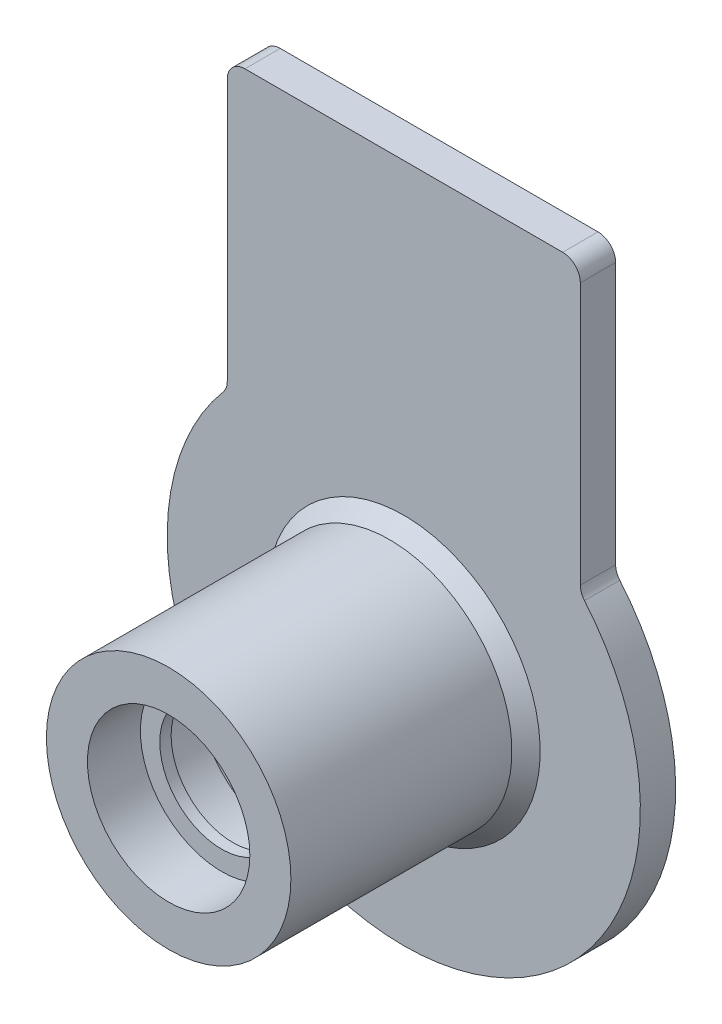
SolidWorks part; units mm, degrees
ref_plane "Front Plane" through (0, 0, 0) normal (0, 0, 1) x (1, 0, 0)
ref_plane "Top Plane" through (0, 0, 0) normal (0, 1, 0) x (1, 0, 0)
ref_plane "Right Plane" through (0, 0, 0) normal (1, 0, 0) x (0, 0, -1)
sketch "Sketch2" plane through (0, 0, 0) normal (0, 1, 0) x (1, 0, 0)
  line L0 (-3.5, -12.32) -> (-3.5, -11.68)
  line L1 (-3.5, -11.68) -> (-4.925, -11.2)
  line L2 (-4.925, -11.2) -> (-4.925, -8.7)
  line L3 (-4.925, -8.7) -> (-3.45, -8.7)
  line L4 (-3.45, -8.7) -> (-3.45, -7.5)
  line L5 (-3.45, -7.5) -> (-5, -7.5)
  line L6 (-3.5, -12.32) -> (-6.925, -12.32)
  line L7 (-6.925, -12.32) -> (-6.925, -2)
  line L8 (-5, -7.5) -> (-5, 0)
  line L12 (-13.4, 0) -> (-13.4, -2)
  line L13 (-13.4, -2) -> (-6.925, -2)
  line L14 (0, 0) -> (0, -12.32) construction
  line L15 (13.4, -2) -> (6.925, -2) construction
  line L16 (13.4, 0) -> (13.4, -2) construction
  line L20 (5, -7.5) -> (5, 0) construction
  line L21 (6.925, -12.32) -> (6.925, -2) construction
  line L22 (3.5, -12.32) -> (6.925, -12.32) construction
  line L23 (3.45, -7.5) -> (5, -7.5) construction
  line L24 (3.45, -8.7) -> (3.45, -7.5) construction
  line L25 (4.925, -8.7) -> (3.45, -8.7) construction
  line L26 (4.925, -11.2) -> (4.925, -8.7) construction
  line L27 (3.5, -11.68) -> (4.925, -11.2) construction
  line L28 (3.5, -12.32) -> (3.5, -11.68) construction
  line L31 (-5, 0) -> (-13.4, 0)
  line L34 (5, 0) -> (13.4, 0) construction
other "AlignGroup1"
other "AlignGroup2" parameters "D1"=6.1239, "D2"=15.6, "D3"=6.4543, "D4"=0.8, "D5"=10.0543, "D6"=6, "D7"=8.1501, "D8"=3.5773, "D9"=31.118, "D10"=2.5, "D11"=0.8, "D12"=5.3492, "D13"=1.7, "D14"=0.819, "D15"=0.3, "D16"=2.2
revolve "Revolve1" add sketch "Sketch2" angle 360 about L14
sketch "Sketch3" plane through (0, 0, 2) normal (0, 0, 1) x (1, 0, 0)
  line L0 (10, 8.9196) -> (10, 25.1216)
  line L1 (10, 25.1216) -> (-10, 25.1216)
  line L2 (-10, 25.1216) -> (-10, 8.9196)
  line L3 (0, 0) -> (-8, 8.1216) construction
  line L4 (-8, 8.1216) -> (-10, 8.1216) construction
  circle A0 centre (0, 0) radius 13.4 construction
  arc A1 (-10, 8.9196) -> (10, 8.9196) centre (0, 0) cw
  circle A2 centre (0, 0) radius 11.4 construction
  dimension "D2" = 22.8
  dimension "D1" = 20
  dimension "D3" = 2
  dimension "D4" = 17
extrude "Boss-Extrude1" add sketch "Sketch3" against normal up to surface (2 mm away) up to face at (-13.4, 0, 0)
fillet "Fillet2" radius 1 4 edges at (10, 8.9196, 1) (10, 25.1216, 1) (-10, 8.9196, 1) (-10, 25.1216, 1)
chamfer "Chamfer1" distance 0.8 angle 45 1 edges at (-6.925, 0, 2)
sketch "Sketch4" plane through (0, 0, 12.32) normal (0, 0, 1) x (1, 0, 0)
  circle A0 centre (0, 0) radius 4.6
  circle A1 centre (0, 0) radius 6.925 construction
  circle A2 centre (0, 0) radius 6.925
  dimension "D1" = 9.2
extrude "Boss-Extrude2" add sketch "Sketch4" along normal blind 3
